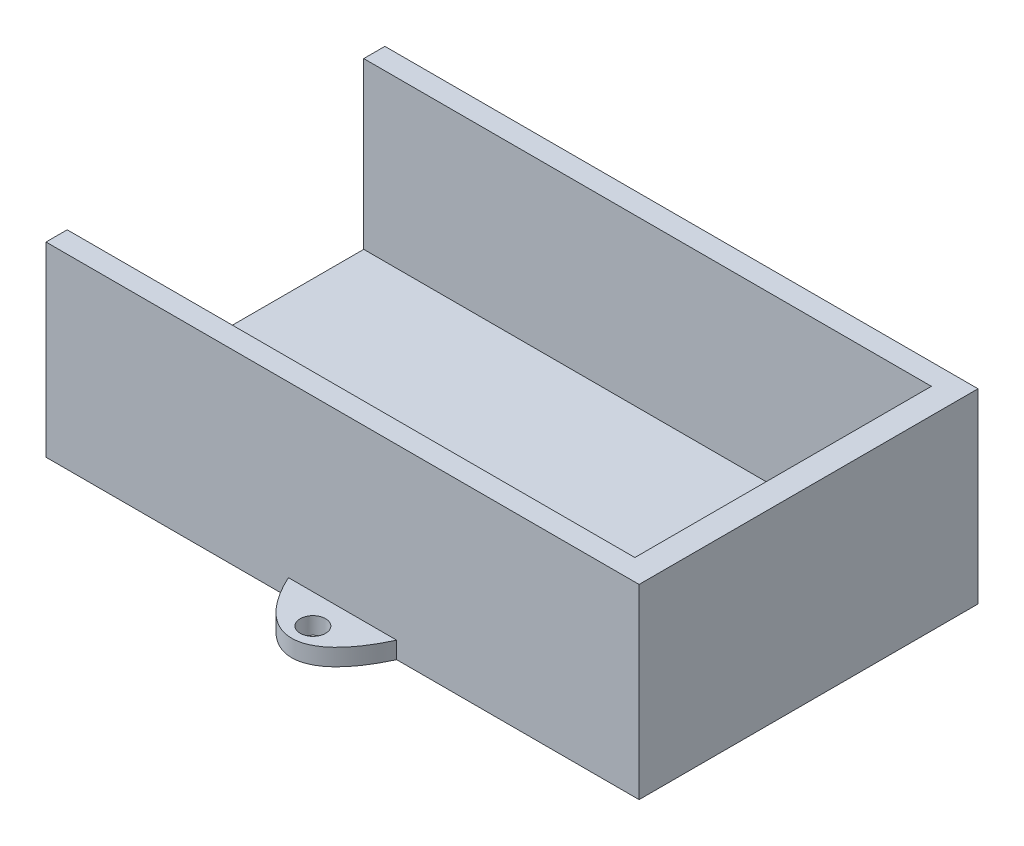
SolidWorks part; units mm, degrees
ref_plane "Front Plane" through (0, 0, 0) normal (0, 0, 1) x (1, 0, 0)
ref_plane "Top Plane" through (0, 0, 0) normal (0, 1, 0) x (1, 0, 0)
ref_plane "Right Plane" through (0, 0, 0) normal (1, 0, 0) x (0, 0, -1)
sketch "Çizim1" plane through (0, 0, 0) normal (0, 1, 0) x (1, 0, 0)
  line L1 (32.7674, -13.0184) -> (-37.2326, -13.0184)
  line L2 (32.7674, -13.0184) -> (32.7674, 26.9816)
  line L3 (32.7674, 26.9816) -> (-37.2326, 26.9816)
  line L4 (-37.2326, -13.0184) -> (-37.2326, 26.9816)
extrude "Yükseklik-Ekstrüzyon2" add sketch "Çizim1" along normal blind 25 contours L2 L1 L4 L3
sketch "Çizim2" plane through (-37.2326, 0, 0) normal (-1, 0, 0) x (0, 0, 1)
  line L0 (-26.9816, 25) -> (13.0184, 0) construction
  line L2 (-24.4816, 2.5) -> (10.5184, 2.5)
  line L3 (-24.4816, 2.5) -> (-24.4816, 22.5)
  line L4 (-24.4816, 22.5) -> (10.5184, 22.5)
  line L5 (10.5184, 2.5) -> (10.5184, 22.5)
  line L6 (-24.4816, 2.5) -> (10.5184, 22.5) construction
  line L7 (-24.4816, 22.5) -> (10.5184, 2.5) construction
  point P4 (-6.9816, 12.5)
extrude "Kes-Ekstrüzyon2" cut sketch "Çizim2" against normal blind 67
sketch "Çizim3" plane through (0, 25, 0) normal (0, 1, 0) x (1, 0, 0)
  line L1 (-37.2326, 26.9816) -> (32.7674, 26.9816)
  line L2 (-37.2326, 26.9816) -> (-37.2326, -13.0184)
  line L3 (-37.2326, -13.0184) -> (32.7674, -13.0184)
  line L4 (32.7674, 26.9816) -> (32.7674, -13.0184)
extrude "Kes-Ekstrüzyon3" cut sketch "Çizim3" against normal blind 3
sketch "Çizim4" plane through (0, 0, 0) normal (0, -1, 0) x (1, 0, 0)
  line L0 (-37.2326, 13.0184) -> (32.7674, -26.9816) construction
  circle A0 centre (-2.2326, 16.5184) radius 1.5
  ellipse E0 centre (-2.2326, -6.9816) end of major axis (-2.2326, 19.0184) minor radius 10
extrude "Yükseklik-Ekstrüzyon3" add sketch "Çizim4" against normal blind 2 contours E0
sketch "Çizim5" plane through (0, 2, 0) normal (0, 1, 0) x (1, 0, 0)
  circle A0 centre (-2.2326, -16.5184) radius 1.5
  circle A1 centre (-2.2326, 30.4816) radius 1.5
extrude "Kes-Ekstrüzyon5" cut sketch "Çizim5" against normal blind 16 contours A0 | A1
